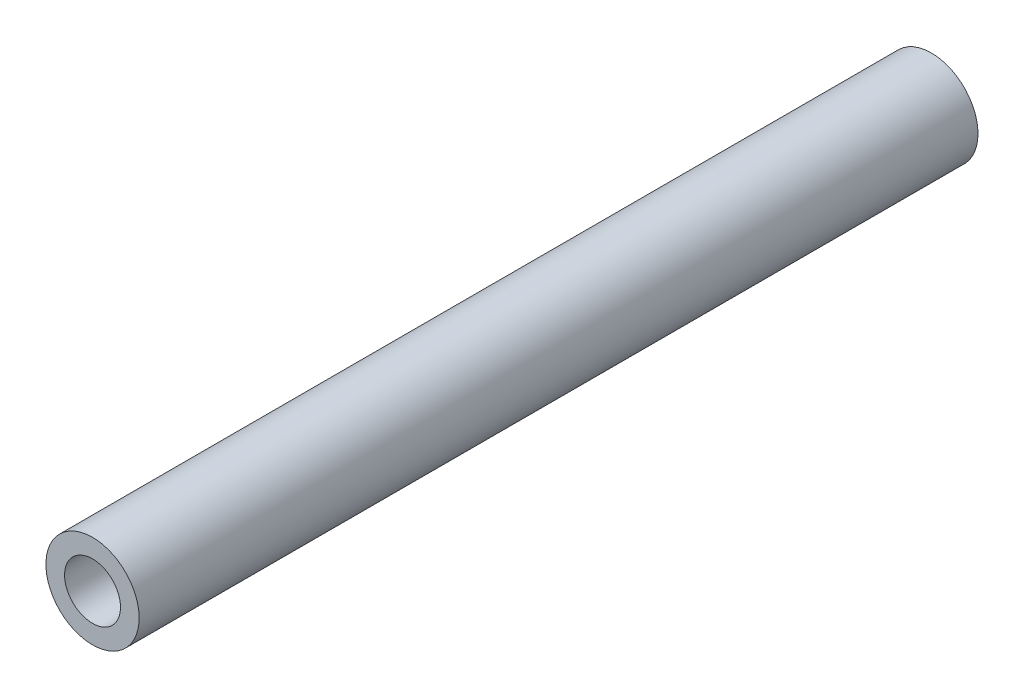
SolidWorks part; units mm, degrees
ref_plane "前视基准面" through (0, 0, 0) normal (0, 0, 1) x (1, 0, 0)
ref_plane "上视基准面" through (0, 0, 0) normal (0, 1, 0) x (1, 0, 0)
ref_plane "右视基准面" through (0, 0, 0) normal (1, 0, 0) x (0, 0, -1)
sketch "草图1" plane through (0, 0, 0) normal (0, 0, 1) x (1, 0, 0)
  circle A0 centre (0, 0) radius 2.5
  circle A1 centre (0, 0) radius 1.5
  dimension "D1" = 3
  dimension "D2" = 5
extrude "凸台-拉伸1" add sketch "草图1" along normal mid plane 45
